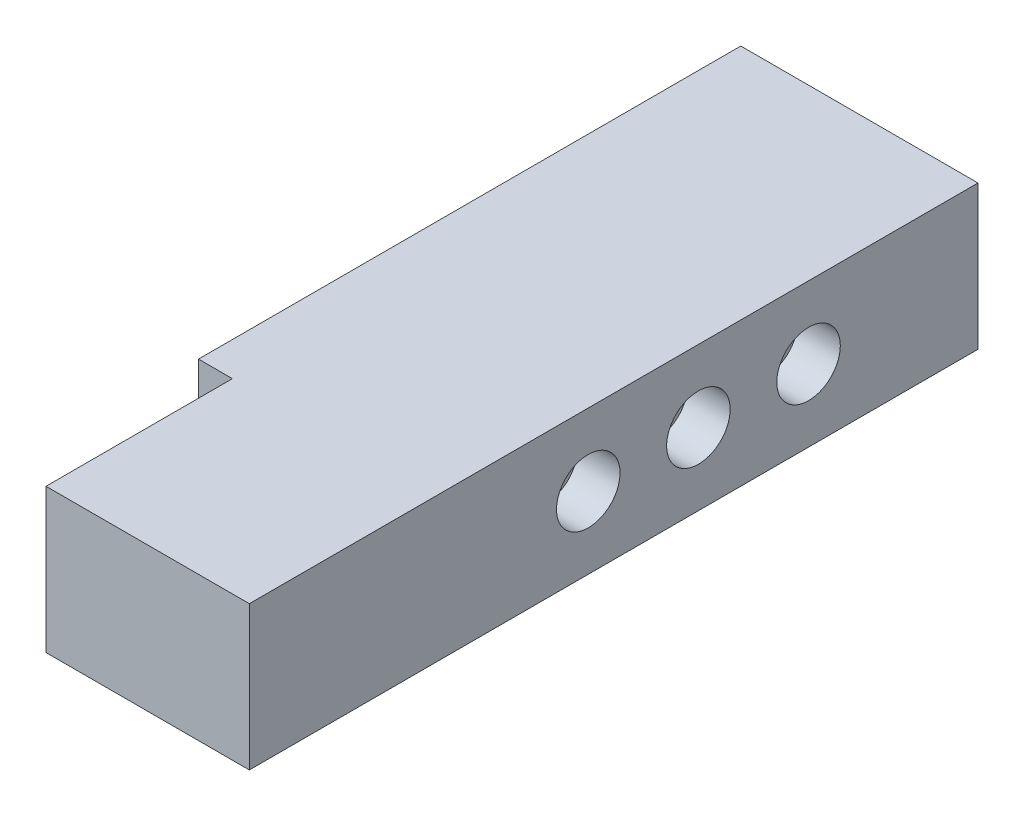
SolidWorks part; units mm, degrees
material "PE High Density"
ref_plane "Front Plane" through (0, 0, 0) normal (0, 0, 1) x (1, 0, 0)
ref_plane "Top Plane" through (0, 0, 0) normal (0, 1, 0) x (1, 0, 0)
ref_plane "Right Plane" through (0, 0, 0) normal (1, 0, 0) x (0, 0, -1)
sketch "Sketch1" plane through (0, 0, 0) normal (0, 0, 1) x (1, 0, 0)
  line L1 (0, 0) -> (35.56, 0)
  line L2 (0, 0) -> (0, 21.59)
  line L3 (0, 21.59) -> (35.56, 21.59)
  line L4 (35.56, 0) -> (35.56, 21.59)
  dimension "D1" = 21.59
  dimension "D2" = 35.56
extrude "Boss-Extrude1" add sketch "Sketch1" along normal blind 81.28
sketch "Sketch2" plane through (0, 0, 81.28) normal (0, 0, 1) x (1, 0, 0)
  line L0 (0, 0) -> (35.56, 0) construction
  line L1 (35.56, 21.59) -> (5.08, 21.59)
  line L2 (35.56, 21.59) -> (35.56, 0)
  line L3 (35.56, 0) -> (5.08, 0)
  line L4 (5.08, 21.59) -> (5.08, 0)
  dimension "D1" = 30.48
extrude "Boss-Extrude2" add sketch "Sketch2" along normal blind 27.94
sketch "Sketch3" plane through (35.56, 0, 0) normal (1, 0, 0) x (0, 0, -1)
  line L0 (0, 10.795) -> (-109.22, 10.795) construction
  line L1 (0, 0) -> (0, 21.59) construction
  line L2 (-109.22, 0) -> (-109.22, 21.59) construction
  circle A0 centre (-25.4, 10.795) radius 4.7625
  circle A1 centre (-41.91, 10.795) radius 4.7625
  circle A2 centre (-58.42, 10.795) radius 4.7625
  dimension "D1" = 9.525
  dimension "D2" = 9.525
  dimension "D3" = 9.525
  dimension "D4" = 25.4
  dimension "D5" = 16.51
  dimension "D6" = 16.51
extrude "Cut-Extrude1" cut sketch "Sketch3" against normal blind 6.35
sketch "Sketch4" plane through (0, 0, 0) normal (-1, 0, 0) x (0, 0, 1)
  line L0 (0, 10.795) -> (81.28, 10.795) construction
  line L1 (0, 21.59) -> (0, 0) construction
  line L2 (81.28, 21.59) -> (81.28, 0) construction
  circle A0 centre (33.655, 10.795) radius 4.7625
  circle A1 centre (50.165, 10.795) radius 4.7625
  dimension "D1" = 9.525
  dimension "D2" = 9.525
  dimension "D3" = 33.655
  dimension "D4" = 16.51
extrude "Cut-Extrude2" cut sketch "Sketch4" against normal blind 6.35
